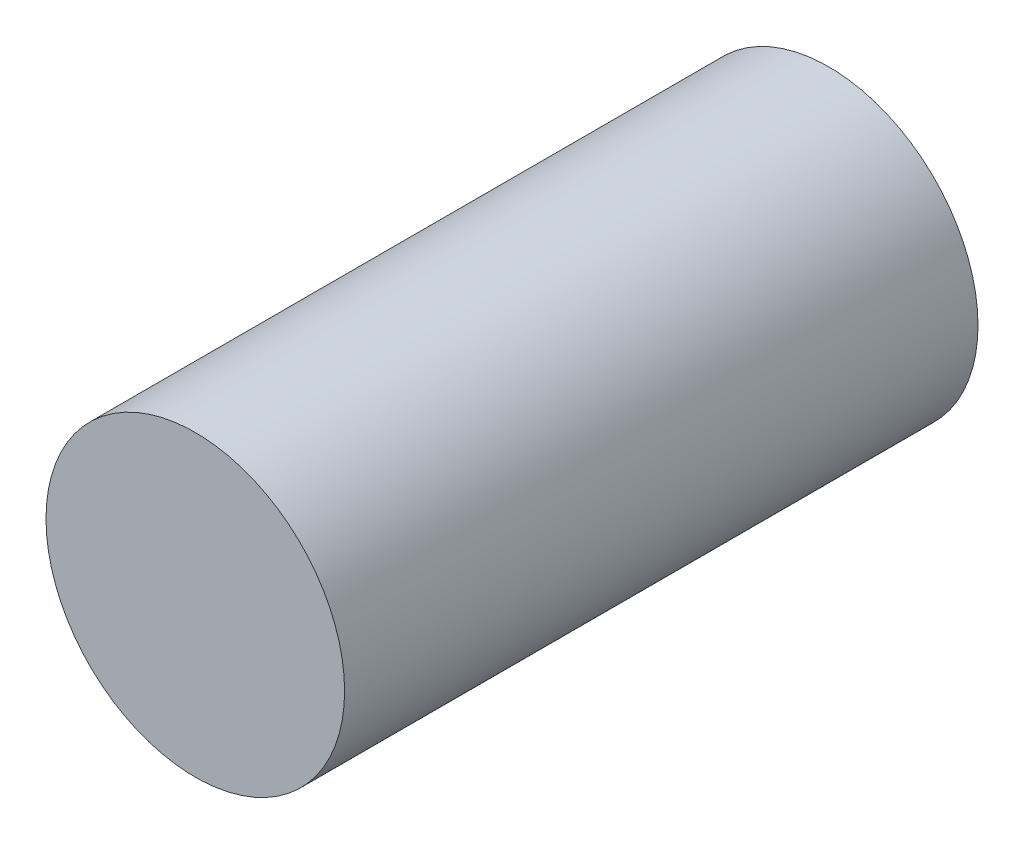
SolidWorks part; units mm, degrees
ref_plane "Front Plane" through (0, 0, 0) normal (0, 0, 1) x (1, 0, 0)
ref_plane "Top Plane" through (0, 0, 0) normal (0, 1, 0) x (1, 0, 0)
ref_plane "Right Plane" through (0, 0, 0) normal (1, 0, 0) x (0, 0, -1)
sketch "Sketch1" plane through (0, 0, 0) normal (0, 0, 1) x (1, 0, 0)
  circle A0 centre (0, 0) radius 16.5
  dimension "D1" = 33
extrude "Boss-Extrude1" add sketch "Sketch1" along normal blind 70
